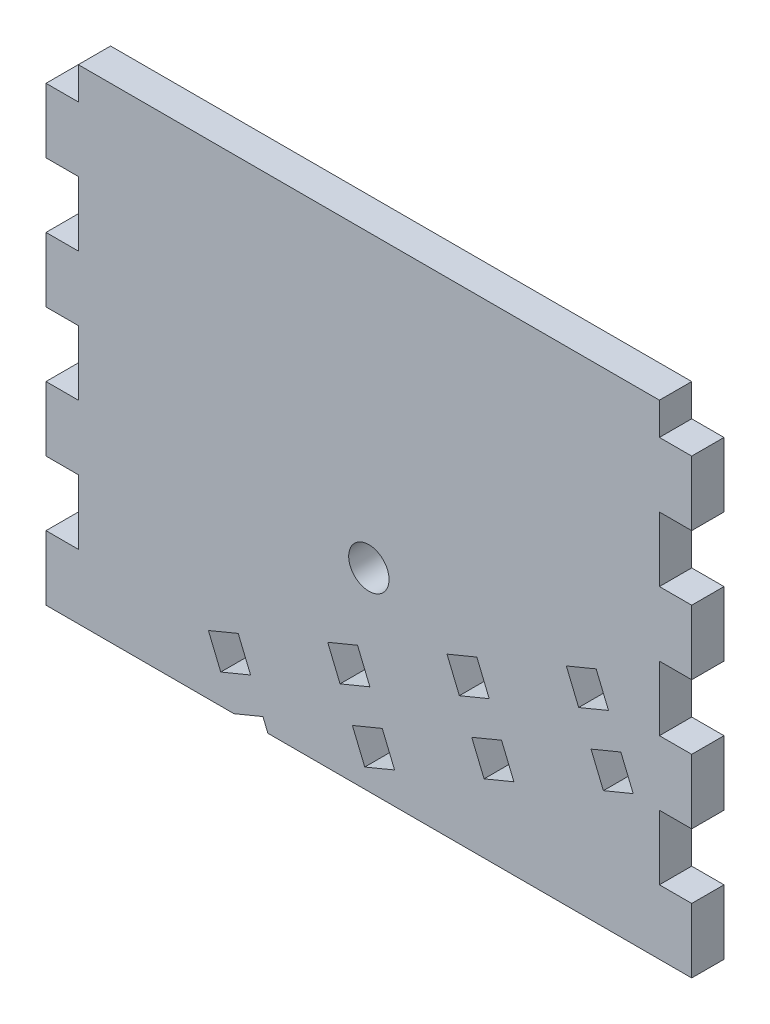
SolidWorks part; units mm, degrees
material "Pine"
ref_plane "Front Plane" through (0, 0, 0) normal (0, 0, 1) x (1, 0, 0)
ref_plane "Top Plane" through (0, 0, 0) normal (0, 1, 0) x (1, 0, 0)
ref_plane "Right Plane" through (0, 0, 0) normal (1, 0, 0) x (0, 0, -1)
sketch "Sketch1" plane through (0, 0, 0) normal (0, 0, 1) x (1, 0, 0)
  line L1 (0, 0) -> (127, 0)
  line L2 (0, 0) -> (0, 95.25)
  line L3 (0, 95.25) -> (127, 95.25)
  line L4 (127, 0) -> (127, 95.25)
  dimension "D1" = 127
  dimension "D2" = 95.25
extrude "Boss-Extrude1" add sketch "Sketch1" along normal blind 6.35
sketch "Sketch2" plane through (0, 0, 6.35) normal (0, 0, 1) x (1, 0, 0)
  line L0 (0, 95.25) -> (0, 0) construction
  line L1 (0, 0) -> (127, 0) construction
  circle A0 centre (63.5, 38.1) radius 3.9687
  dimension "D3" = 7.9375
  dimension "D1" = 63.5
  dimension "D2" = 38.1
extrude "Cut-Extrude1" cut sketch "Sketch2" against normal through all
sketch "Sketch3" plane through (0, 0, 6.35) normal (0, 0, 1) x (1, 0, 0)
  line L0 (0, 95.25) -> (0, 0) construction
  line L1 (0, 12.7) -> (6.35, 12.7)
  line L2 (0, 12.7) -> (0, 25.4)
  line L3 (0, 25.4) -> (6.35, 25.4)
  line L4 (6.35, 12.7) -> (6.35, 25.4)
  dimension "D1" = 6.35
  dimension "D2" = 12.7
  dimension "D3" = 12.7
extrude "Cut-Extrude2" cut sketch "Sketch3" against normal through all
sketch "Sketch4" plane through (0, 0, 6.35) normal (0, 0, 1) x (1, 0, 0)
  line L0 (127, 0) -> (127, 95.25) construction
  line L1 (127, 12.7) -> (120.65, 12.7)
  line L2 (127, 12.7) -> (127, 25.4)
  line L3 (127, 25.4) -> (120.65, 25.4)
  line L4 (120.65, 12.7) -> (120.65, 25.4)
  line L5 (6.35, 12.7) -> (6.35, 25.4) construction
  line L6 (0, 12.7) -> (6.35, 12.7) construction
extrude "Cut-Extrude3" cut sketch "Sketch4" against normal through all
pattern_linear "LPattern1" count 4 spacing 25.4 along (0, 1, 0) of "Cut-Extrude2", "Cut-Extrude3"
sketch "Sketch5" plane through (0, 0, 6.35) normal (0, 0, 1) x (1, 0, 0)
  line L0 (120.65, 38.1) -> (28.6685, 0) construction
  line L1 (0, 0) -> (127, 0) construction
  line L2 (106.4867, 39.1066) -> (111.3468, 27.3733) construction
  line L3 (102.3384, 40.8249) -> (104.7684, 34.9582)
  line L4 (102.3384, 40.8249) -> (108.205, 43.2549)
  line L5 (104.7684, 34.9582) -> (110.635, 37.3883)
  line L6 (108.205, 43.2549) -> (110.635, 37.3883)
  line L7 (102.3384, 40.8249) -> (110.635, 37.3883) construction
  line L8 (104.7684, 34.9582) -> (108.205, 43.2549) construction
  line L9 (109.6285, 23.2249) -> (107.1984, 29.0916)
  line L10 (109.6285, 23.2249) -> (115.4951, 25.655)
  line L11 (107.1984, 29.0916) -> (113.0651, 31.5216)
  line L12 (115.4951, 25.655) -> (113.0651, 31.5216)
  line L13 (109.6285, 23.2249) -> (113.0651, 31.5216) construction
  line L14 (107.1984, 29.0916) -> (115.4951, 25.655) construction
  point P8 (108.9167, 33.2399)
  dimension "D1" = 6.35
  dimension "D2" = 6.35
  dimension "D3" = 6.35
  dimension "D4" = 12.7
  dimension "D5" = 22.5
extrude "Cut-Extrude4" cut sketch "Sketch5" against normal through all
pattern_linear "LPattern2" count 4 spacing 25.4 along (-0.9239, -0.3827, 0) of "Cut-Extrude4"
